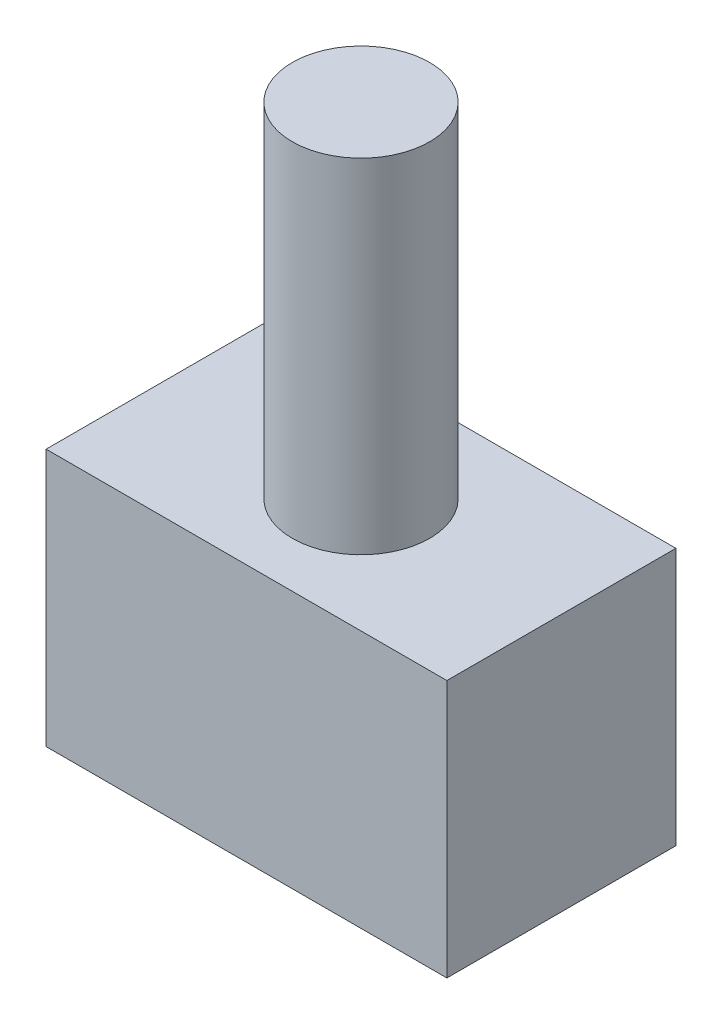
SolidWorks part; units mm, degrees
ref_plane "Front Plane" through (0, 0, 0) normal (0, 0, 1) x (1, 0, 0)
ref_plane "Top Plane" through (0, 0, 0) normal (0, 1, 0) x (1, 0, 0)
ref_plane "Right Plane" through (0, 0, 0) normal (1, 0, 0) x (0, 0, -1)
sketch "Sketch1" plane through (0, 0, 0) normal (0, 1, 0) x (1, 0, 0)
  line L0 (0, 10) -> (35, 10) construction
  line L1 (0, 20) -> (35, 20)
  line L2 (0, 20) -> (0, 0)
  line L3 (0, 0) -> (35, 0)
  line L4 (35, 20) -> (35, 0)
  line L5 (17.5, 0) -> (17.5, 20) construction
  point P9 (17.5, 10)
  dimension "D1" = 20
  dimension "D2" = 35
extrude "Extrude1" add sketch "Sketch1" against normal blind 22.5
sketch "Sketch2" plane through (0, 0, 0) normal (0, 1, 0) x (1, 0, 0)
  line L0 (0, 10) -> (35, 10) construction
  line L1 (0, 20) -> (0, 0) construction
  line L2 (35, 0) -> (35, 20) construction
  line L3 (17.5, 20) -> (17.5, 0) construction
  line L4 (35, 20) -> (0, 20) construction
  line L5 (0, 0) -> (35, 0) construction
  circle A0 centre (17.5, 10) radius 6
  point P12 (17.5, 10)
  dimension "D1" = 12
extrude "Extrude2" add sketch "Sketch2" along normal blind 30
